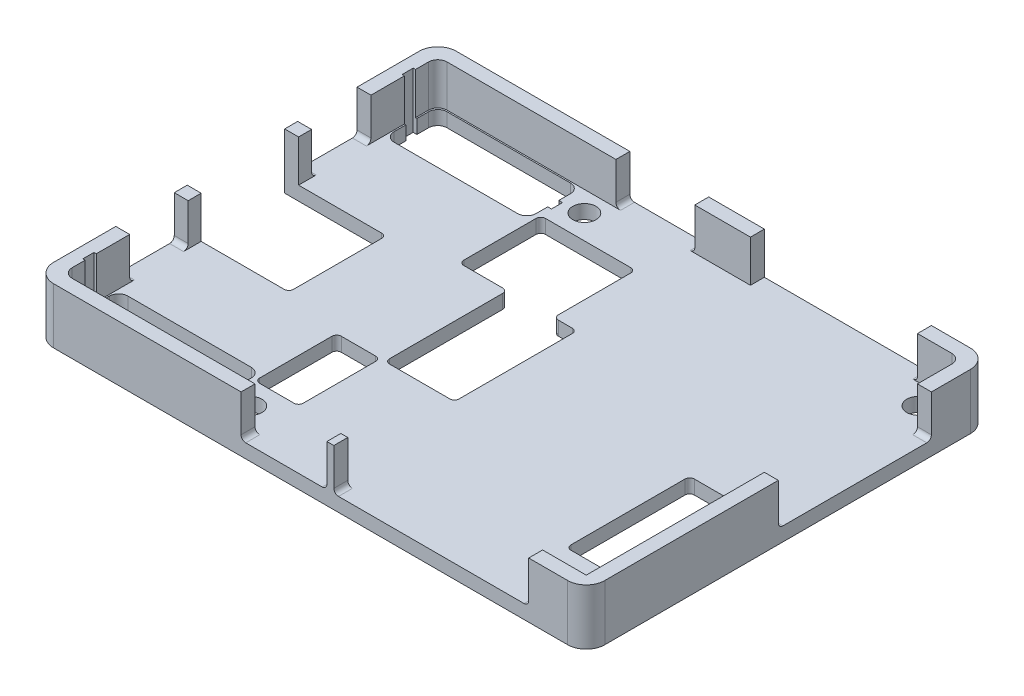
SolidWorks part; units mm, degrees
ref_plane "前视基准面" through (0, 0, 0) normal (0, 0, 1) x (1, 0, 0)
ref_plane "上视基准面" through (0, 0, 0) normal (0, 1, 0) x (1, 0, 0)
ref_plane "右视基准面" through (0, 0, 0) normal (1, 0, 0) x (0, 0, -1)
sketch "草图1" plane through (0, 0, 0) normal (0, 1, 0) x (1, 0, 0)
  line L1 (-29.7, 21.7) -> (29.7, 21.7)
  line L2 (-29.7, 21.7) -> (-29.7, -21.7)
  line L3 (-29.7, -21.7) -> (29.7, -21.7)
  line L4 (29.7, 21.7) -> (29.7, -21.7)
  line L5 (-29.7, 21.7) -> (29.7, -21.7) construction
  line L6 (-29.7, -21.7) -> (29.7, 21.7) construction
  point P0 (0, 0)
extrude "凸台-拉伸1" add sketch "草图1" along normal blind 6
sketch "草图2" plane through (0, 6, 0) normal (0, 1, 0) x (1, 0, 0)
  line L1 (-28.2, 20.2) -> (28.2, 20.2)
  line L2 (-28.2, 20.2) -> (-28.2, -20.2)
  line L3 (-28.2, -20.2) -> (28.2, -20.2)
  line L4 (28.2, 20.2) -> (28.2, -20.2)
  line L5 (-28.2, 20.2) -> (28.2, -20.2) construction
  line L6 (-28.2, -20.2) -> (28.2, 20.2) construction
  point P0 (0, 0)
extrude "切除-拉伸1" cut sketch "草图2" against normal blind 4.5
sketch "草图3" plane through (0, 1.5, 0) normal (0, 1, 0) x (1, 0, 0)
  line L0 (29.7, 0) -> (-10.2, 0) construction
  line L1 (29.7, -21.7) -> (29.7, 21.7) construction
  line L2 (-10.2, 0) -> (-10.2, -16.7558) construction
  line L3 (0, -21.7) -> (0, -18) construction
  line L4 (-29.7, -21.7) -> (29.7, -21.7) construction
  line L5 (25.8, 18) -> (29.7, 18) construction
  line L6 (0, 21.7) -> (0, 18) construction
  line L7 (29.7, 21.7) -> (-29.7, 21.7) construction
  line L8 (25.8, 18) -> (-10.2, 18) construction
  line L9 (25.8, 18) -> (25.8, -18) construction
  line L10 (25.8, -18) -> (-10.2, -18) construction
  circle A0 centre (-10.2, -18) radius 1.25
  circle A1 centre (-10.2, 18) radius 1.25
  circle A2 centre (25.8, 18) radius 1.25
  circle A3 centre (25.8, -18) radius 1.25
extrude "切除-拉伸2" cut sketch "草图3" against normal through all
sketch "草图4" plane through (0, 1.5, 0) normal (0, 1, 0) x (1, 0, 0)
  line L0 (-29.7, 21.7) -> (-29.7, 5.2) construction
  line L1 (-29.7, 21.7) -> (-29.7, -21.7) construction
  line L2 (-29.7, 5.2) -> (-18.75, 5.2)
  line L3 (-29.7, -5.3) -> (-29.7, -21.7) construction
  line L5 (-29.7, -5.3) -> (-18.75, -5.3)
  line L6 (-18.75, -5.3) -> (-18.75, 5.2)
  line L7 (-29.7, 5.2) -> (-29.7, -5.3)
extrude "切除-拉伸3" cut sketch "草图4" against normal through all and the other way through all
sketch "草图5" plane through (-29.7, 0, 0) normal (-1, 0, 0) x (0, 0, 1)
  line L0 (-21.7, 0) -> (-21.7, -5) construction
  line L1 (-21.7, -5) -> (-13, -5) construction
  line L2 (-13, -5) -> (-6.6, -5) construction
  line L4 (13, -5) -> (6.7, -5) construction
  line L9 (21.7, 0) -> (21.7, -5) construction
  line L10 (21.7, -5) -> (13, -5) construction
  line L21 (-13, 1.5) -> (-13, 6)
  line L22 (-18, 1.5) -> (18, 1.5) construction
  line L23 (20.2, 6) -> (-20.2, 6) construction
  line L24 (-13, 6) -> (-6.6, 6)
  line L25 (-6.6, 6) -> (-6.6, 1.5)
  line L26 (-6.6, 1.5) -> (-13, 1.5)
  line L27 (6.7, 1.5) -> (6.7, 6)
  line L28 (-20.2, 6) -> (20.2, 6) construction
  line L29 (6.7, 6) -> (13, 6)
  line L30 (13, 6) -> (13, 1.5)
  line L31 (13, 1.5) -> (6.7, 1.5)
  line L32 (5.3, 0) -> (5.3, -5) construction
  line L33 (5.3, -5) -> (6.7, -5) construction
  line L34 (-5.2, 0) -> (-5.2, -5) construction
  line L35 (-5.2, -5) -> (-6.6, -5) construction
  line L36 (-5.2, -5) -> (5.3, -5) construction
extrude "切除-拉伸4" cut sketch "草图5" against normal blind 4.5
sketch "草图8" plane through (0, 1.5, 0) normal (0, 1, 0) x (1, 0, 0)
  line L0 (-29.7, -21.7) -> (-34.7, -21.7) construction
  line L1 (-34.7, -21.7) -> (-34.7, -20.05) construction
  line L2 (-34.7, -20.05) -> (-34.7, -14.35) construction
  line L3 (-34.7, -20.05) -> (-29.7, -20.05) construction
  line L4 (-29.7, 21.7) -> (-29.7, -21.7) construction
  line L5 (-34.7, -14.35) -> (-29.7, -14.35) construction
  line L6 (-29.7, -21.7) -> (-29.7, -26.7) construction
  line L7 (-29.7, -26.7) -> (-12.35, -26.7) construction
  line L8 (-29.7, -26.7) -> (-28.05, -26.7) construction
  line L9 (-29.7, -26.7) -> (-28.45, -26.7) construction
  line L10 (-33.7101, -21.7) -> (-33.7101, -17.8) construction
  line L11 (-33.7101, -21.7) -> (-33.7101, -16.6) construction
  line L12 (-28.05, -26.7) -> (-28.05, -14.35) construction
  line L13 (-29.7, -20.05) -> (-12.35, -20.05) construction
  line L15 (-28.05, 14.35) -> (-28.05, 16.6)
  line L19 (-28.2, -20.2) -> (28.2, -20.2) construction
  line L20 (-28.05, -20.05) -> (-12.75, -20.05)
  line L21 (-12.75, -14.35) -> (-28.05, -14.35)
  line L23 (-28.45, -17.8) -> (-28.05, -17.8)
  line L24 (-28.45, -17.8) -> (-28.45, -16.6)
  line L25 (-28.45, -16.6) -> (-28.05, -16.6)
  line L26 (-28.05, -20.05) -> (-28.05, -17.8)
  line L27 (-28.05, -16.6) -> (-28.05, -14.35)
  line L28 (-12.35, -17.8) -> (-12.75, -17.8)
  line L29 (-12.35, -17.8) -> (-12.35, -16.6)
  line L30 (-12.35, -16.6) -> (-12.75, -16.6)
  line L31 (-12.75, -17.8) -> (-12.75, -20.05)
  line L32 (-12.75, -16.6) -> (-12.75, -14.35)
  line L33 (-29.7, 21.7) -> (-34.7, 21.7) construction
  line L34 (-34.7, 21.7) -> (-34.7, 20.05) construction
  line L35 (-34.7, 21.7) -> (-34.7, 14.35) construction
  line L36 (-33.7101, 21.7) -> (-33.7101, 17.8) construction
  line L37 (-34.7, 21.7) -> (-36.7, 21.7) construction
  line L38 (-36.7, 21.7) -> (-36.7, 16.6) construction
  line L39 (-34.7, 20.05) -> (-12.35, 20.05) construction
  line L40 (-28.05, -14.35) -> (-28.05, 53.9022) construction
  line L41 (-28.05, 20.05) -> (-12.75, 20.05)
  line L43 (-12.75, 20.05) -> (-12.75, 17.8)
  line L44 (-12.75, 17.8) -> (-12.35, 17.8)
  line L45 (-12.35, 17.8) -> (-12.35, 16.6)
  line L46 (-12.35, 16.6) -> (-12.75, 16.6)
  line L47 (-12.75, 16.6) -> (-12.75, 14.35)
  line L48 (-12.75, 14.35) -> (-28.05, 14.35)
  line L49 (-28.05, 16.6) -> (-28.45, 16.6)
  line L50 (-28.45, 16.6) -> (-28.45, 17.8)
  line L51 (-28.45, 17.8) -> (-28.05, 17.8)
  line L52 (-28.05, 17.8) -> (-28.05, 20.05)
extrude "切除-拉伸5" cut sketch "草图8" against normal through all both and the other way through all
sketch "草图9" plane through (0, 1.5, 0) normal (0, 1, 0) x (1, 0, 0)
  line L0 (-29.7, 21.7) -> (-29.7, 26.7) construction
  line L1 (-29.7, 26.7) -> (-12.3, 26.7) construction
  line L2 (-29.7, 21.7) -> (29.7, 21.7) construction
  line L3 (-29.7, 26.7) -> (-29.7, 28.7) construction
  line L4 (-29.7, 28.7) -> (-2.1, 28.7) construction
  line L5 (-29.7, 21.7) -> (-34.7, 21.7) construction
  line L6 (-36.7, 21.7) -> (-36.7, 6.6) construction
  line L7 (-29.7, 28.7) -> (-29.7, 30.7) construction
  line L8 (-12.3, 15.4) -> (-12.3, 6.6)
  line L9 (-34.7, 21.7) -> (-34.7, 15.4) construction
  line L10 (-34.7, 21.7) -> (-36.7, 21.7) construction
  line L11 (-12.3, 6.6) -> (-2.1, 6.6)
  line L12 (-2.1, 6.6) -> (-2.1, 15.4)
  line L13 (-2.1, 15.4) -> (-12.3, 15.4)
  line L14 (-29.7, 30.7) -> (-7.6, 30.7) construction
  line L15 (-12.3, 26.7) -> (-12.3, 23.3714) construction
  line L16 (-7.6, 30.7) -> (-7.6, 26.7) construction
  line L17 (-29.7, -21.7) -> (-34.7, -21.7) construction
  line L18 (-34.7, -21.7) -> (-36.7, -21.7) construction
  line L19 (-36.7, -21.7) -> (-36.7, -6.6) construction
  line L20 (-34.7, -21.7) -> (-34.7, -15.4) construction
  line L21 (-29.7, 21.7) -> (-29.7, -21.7) construction
  line L22 (-12.3, -15.4) -> (-7.6, -15.4)
  line L23 (-7.6, -15.4) -> (-7.6, -6.6)
  line L24 (-7.6, -6.6) -> (-12.3, -6.6)
  line L25 (-12.3, -6.6) -> (-12.3, -15.4)
extrude "切除-拉伸6" cut sketch "草图9" against normal through all both and the other way through all
sketch "草图10" plane through (0, 1.5, 0) normal (0, 1, 0) x (1, 0, 0)
  line L0 (29.7, -21.7) -> (29.7, -26.784) construction
  line L1 (29.7, 21.7) -> (29.7, -21.7) construction
  line L2 (29.7, -26.784) -> (29.7, -28.784) construction
  line L3 (29.7, -26.784) -> (28.05, -26.784) construction
  line L4 (29.7, -28.784) -> (20.05, -28.784) construction
  line L5 (-29.7, -21.7) -> (29.7, -21.7) construction
  line L6 (29.7, -21.7) -> (34.7, -21.7) construction
  line L7 (34.7, -21.7) -> (36.7, -21.7) construction
  line L8 (34.7, -21.7) -> (34.7, -14.2) construction
  line L9 (36.7, -21.7) -> (36.7, -0.9) construction
  line L10 (28.05, -14.2) -> (20.05, -14.2)
  line L11 (20.05, -14.2) -> (20.05, -0.9)
  line L12 (20.05, -0.9) -> (28.05, -0.9)
  line L13 (28.05, -0.9) -> (28.05, -14.2)
  line L14 (28.05, -14.2) -> (36.7, -14.2) construction
  line L15 (28.05, -0.9) -> (36.7, -0.9) construction
  line L16 (28.05, -26.784) -> (28.05, -0.9) construction
  line L17 (20.05, -14.2) -> (20.05, -28.784) construction
extrude "切除-拉伸7" cut sketch "草图10" against normal through all both and the other way through all
fillet "圆角1" radius 2 4 edges at (29.7, 3, 21.7) (-29.7, 3, 21.7) (-29.7, 3, -21.7) (29.7, 3, -21.7)
sketch "草图11" plane through (0, 0, -21.7) normal (0, 0, -1) x (-1, 0, 0)
  line L0 (29.7, 6) -> (29.7, 11) construction
  line L1 (29.7, 11) -> (9, 11) construction
  line L2 (9, 11) -> (0.5, 11) construction
  line L3 (0.5, 11) -> (-5.5, 11) construction
  line L4 (-5.5, 11) -> (-23.5, 11) construction
  line L5 (-23.5, 11) -> (-29.7, 11) construction
  line L6 (-29.7, 11) -> (-29.7, 6) construction
  line L7 (9, 1.5) -> (9, 6)
  line L8 (11.45, 1.5) -> (8.95, 1.5) construction
  line L9 (28.2, 6) -> (-28.2, 6) construction
  line L10 (9, 6) -> (0.5, 6)
  line L11 (0.5, 6) -> (0.5, 1.5)
  line L12 (-25.8, 1.5) -> (10.2, 1.5) construction
  line L13 (0.5, 1.5) -> (9, 1.5)
  line L14 (-5.5, 6) -> (-5.5, 1.5)
  line L15 (-5.5, 1.5) -> (-23.5, 1.5)
  line L16 (-23.5, 1.5) -> (-23.5, 6)
  line L17 (28.2, 6) -> (-28.2, 6) construction
  line L18 (-23.5, 6) -> (-5.5, 6)
extrude "切除-拉伸8" cut sketch "草图11" against normal blind 3
sketch "草图12" plane through (0, 0, 21.7) normal (0, 0, 1) x (1, 0, 0)
  line L0 (-29.7, 0) -> (-29.7, -5) construction
  line L1 (-29.7, -5) -> (-7.5, -5) construction
  line L2 (-7.5, -5) -> (1.75, -5) construction
  line L3 (1.75, -5) -> (2.5, -5) construction
  line L4 (2.5, -5) -> (23.5, -5) construction
  line L5 (23.5, -5) -> (29.7, -5) construction
  line L6 (29.7, -5) -> (29.7, 0) construction
  line L7 (-7.5, 1.5) -> (-7.5, 6)
  line L8 (25.8, 1.5) -> (-10.2, 1.5) construction
  line L9 (-28.2, 6) -> (28.2, 6) construction
  line L10 (-7.5, 6) -> (1.75, 6)
  line L11 (1.75, 6) -> (1.75, 1.5)
  line L12 (1.75, 1.5) -> (-7.5, 1.5)
  line L13 (2.5, 1.5) -> (2.5, 6)
  line L14 (2.5, 6) -> (23.5, 6)
  line L15 (-28.2, 6) -> (28.2, 6) construction
  line L16 (23.5, 6) -> (23.5, 1.5)
  line L17 (23.5, 1.5) -> (2.5, 1.5)
extrude "切除-拉伸9" cut sketch "草图12" against normal blind 3
sketch "草图13" plane through (29.7, 0, 0) normal (1, 0, 0) x (0, 0, -1)
  line L0 (21.7, 0) -> (21.7, -5) construction
  line L1 (21.7, 0) -> (-21.7, 0) construction
  line L2 (21.7, 0) -> (-21.7, 0) construction
  line L3 (-21.7, -5) -> (-1, -5) construction
  line L4 (-1, -5) -> (15.5, -5) construction
  line L5 (15.5, -5) -> (21.7, -5) construction
  line L6 (-21.7, -5) -> (-21.7, 0) construction
  line L16 (-20.2, 6) -> (20.2, 6) construction
  line L17 (-1, 6) -> (15.5, 6)
  line L18 (20.2, 6) -> (-20.2, 6) construction
  line L19 (15.5, 6) -> (15.5, 1.5)
  line L20 (200000, 1.5) -> (-200016.7558, 1.5) construction
  line L21 (15.5, 1.5) -> (-1, 1.5)
  line L22 (-1, 1.5) -> (-1, 6)
extrude "切除-拉伸10" cut sketch "草图13" against normal blind 3
sketch "草图14" plane through (0, 0, 0) normal (0, -1, 0) x (1, 0, 0)
  line L0 (-2.1, -31) -> (-2.1, -11) construction
  line L1 (-2.1, -6.6) -> (-2.1, -15.4) construction
  line L2 (-2.1, -31) -> (0.4, -31) construction
  line L3 (0.4, -31) -> (0.4, 14.2812) construction
  line L4 (-7.1, 6.6) -> (-7.1, -6.6)
  line L5 (-9.95, 6.6) -> (0.4, 6.6) construction
  line L6 (-12.3, -6.6) -> (-2.1, -6.6) construction
  line L9 (-7.1, -6.6) -> (0.4, -6.6)
  line L12 (-7.6, 6.6) -> (-12.3, 6.6) construction
  line L13 (0.4, 6.6) -> (-7.1, 6.6)
  line L14 (0.4, -6.6) -> (0.4, 6.6)
extrude "切除-拉伸11" cut sketch "草图14" against normal blind 10
fillet "圆角2" radius 0.5 18 edges at (-12.3, 0.75, 6.6) (-2.1, 0.75, -15.4) (-18.75, 0.75, -5.2) (-7.6, 0.75, 6.6) (28.05, 0.75, 0.9) (-12.3, 0.75, -6.6) (20.05, 0.75, 14.2) (-18.75, 0.75, 5.3) (-7.6, 0.75, 15.4) (28.05, 0.75, 14.2) (20.05, 0.75, 0.9) (-12.3, 0.75, -15.4) (-12.3, 0.75, 15.4) (-7.1, 0.75, 6.6) (-7.1, 0.75, -6.6) (0.4, 0.75, 6.6) (0.4, 0.75, -6.6) (-2.1, 0.75, -6.6)
fillet "圆角3" radius 1 11 edges at (-28.05, 0.75, 14.35) (-28.05, 0.75, -20.05) (-28.2, 3.75, -20.2) (-12.75, 0.75, -14.35) (-12.75, 0.75, 20.05) (-28.05, 0.75, -14.35) (-28.05, 0.75, 20.05) (-28.2, 3.75, 20.2) (-12.75, 0.75, 14.35) (-12.75, 0.75, -20.05) (28.2, 3.75, -20.2)
fillet "圆角4" radius 0.5 13 edges at (-28.95, 1.5, -13) (-28.95, 1.5, 6.7) (-28.95, 1.5, -6.6) (-28.95, 1.5, 13) (28.95, 1.5, 1) (2.5, 1.5, 20.95) (-7.5, 1.5, 20.95) (-9, 1.5, -20.95) (28.95, 1.5, -15.5) (-0.5, 1.5, -20.95) (23.5, 1.5, -20.95) (23.5, 1.5, 20.95) (1.75, 1.5, 20.95)
